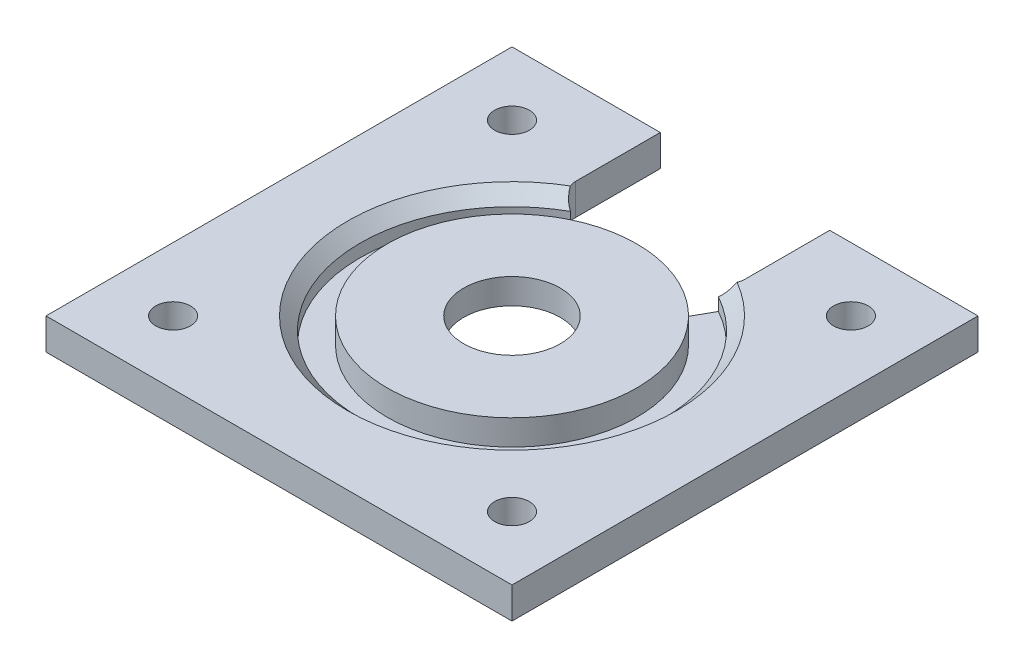
SolidWorks part; units mm, degrees
ref_plane "Front Plane" through (0, 0, 0) normal (0, 0, 1) x (1, 0, 0)
ref_plane "Top Plane" through (0, 0, 0) normal (0, 1, 0) x (1, 0, 0)
ref_plane "Right Plane" through (0, 0, 0) normal (1, 0, 0) x (0, 0, -1)
sketch "Sketch1" plane through (0, 0, 0) normal (0, 0, 1) x (1, 0, 0)
  line L0 (0, 0) -> (5.8, 0)
  line L1 (5.8, 0) -> (5.8, -0.7)
  line L2 (5.8, -0.7) -> (19.7672, -0.7)
  line L3 (19.7672, -0.7) -> (19.7672, 0)
  line L4 (19.7672, 0) -> (9.03, 0)
  line L5 (9.03, 0) -> (9.03, 3)
  line L6 (9.03, 3) -> (0, 3)
  line L7 (0, 3) -> (0, 0)
  line L8 (-5.7, -3.5493) -> (-5.7, 12.6338) construction
  line L9 (-11.4, 3) -> (-11.4, 0)
  line L10 (-20.43, 3) -> (-11.4, 3)
  line L11 (-20.43, 0) -> (-20.43, 3)
  line L12 (-31.1672, 0) -> (-20.43, 0)
  line L13 (-31.1672, -0.7) -> (-31.1672, 0)
  line L14 (-17.2, -0.7) -> (-31.1672, -0.7)
  line L15 (-17.2, 0) -> (-17.2, -0.7)
  line L16 (-11.4, 0) -> (-17.2, 0)
  dimension "D1" = 3
  dimension "D2" = 11.4
  dimension "D3" = 9.03
  dimension "D4" = 0.7
  dimension "D5" = 23
  dimension "D6" = 3
revolve "Revolve1" add sketch "Sketch1" angle 360 about L8
sketch "Sketch2" plane through (0, 0, 0) normal (0, 1, 0) x (1, 0, 0)
  line L5 (-33.2, -27.5) -> (21.8, 27.5) construction
  line L6 (-33.2, 27.5) -> (21.8, -27.5) construction
  line L7 (-33.2, 27.5) -> (21.8, 27.5)
  line L8 (-33.2, 27.5) -> (-33.2, -27.5)
  line L9 (-33.2, -27.5) -> (21.8, -27.5)
  line L10 (21.8, 27.5) -> (21.8, -27.5)
  circle A0 centre (-5.7, 0) radius 17.1
  circle A2 centre (-5.7, 0) radius 5.7 construction
  dimension "D1" = 11.4
  dimension "D2" = 55
  dimension "D3" = 55
extrude "Boss-Extrude1" add sketch "Sketch2" against normal up to surface (0.7 mm away) up to face at (-5.7, -0.7, -25.4672)
sketch "Sketch3" plane through (0, 0, 0) normal (0, 1, 0) x (1, 0, 0)
  line L5 (-33.2, -27.5) -> (21.8, -27.5)
  line L6 (-33.2, -27.5) -> (-33.2, 27.5)
  line L7 (-33.2, 27.5) -> (21.8, 27.5)
  line L8 (21.8, -27.5) -> (21.8, 27.5)
  line L9 (-33.2, -27.5) -> (21.8, 27.5) construction
  line L10 (-33.2, 27.5) -> (21.8, -27.5) construction
  circle A0 centre (-5.7, 0) radius 17.905
  circle A1 centre (-5.7, 0) radius 14.73 construction
  dimension "D1" = 3.175
  dimension "D2" = 55
extrude "Boss-Extrude2" add sketch "Sketch3" along normal up to surface (3 mm away) up to face at (-5.7, 3, -5.7)
sketch "Sketch5" plane through (0, 3, 0) normal (0, 1, 0) x (1, 0, 0)
  line L1 (-25.7, -20) -> (14.3, -20) construction
  line L2 (-25.7, -20) -> (-25.7, 20) construction
  line L3 (-25.7, 20) -> (14.3, 20) construction
  line L4 (14.3, -20) -> (14.3, 20) construction
  line L5 (-25.7, -20) -> (14.3, 20) construction
  line L6 (-25.7, 20) -> (14.3, -20) construction
  circle A0 centre (14.3, 20) radius 2.05
  circle A1 centre (-25.7, 20) radius 2.05
  circle A2 centre (-25.7, -20) radius 2.05
  circle A3 centre (14.3, -20) radius 2.05
  point P0 (-5.7, 0)
  dimension "D1" = 4.1
  dimension "D2" = 40
extrude "Cut-Extrude1" cut sketch "Sketch5" against normal blind 10
chamfer "Chamfer1" distance 1.5 angle 45 1 edges at (-5.7, 3, 17.905)
sketch "Sketch6" plane through (0, 3, 0) normal (0, 1, 0) x (1, 0, 0)
  circle A0 centre (14.3, 20) radius 4.5
  circle A1 centre (14.3, -20) radius 4.5
  circle A2 centre (-25.7, -20) radius 4.5
  circle A3 centre (-25.7, 20) radius 4.5
  point P12 (-5.7, 0)
  dimension "D2" = 9
  dimension "D1" = 4
extrude "Cut-Extrude2" [suppressed] cut sketch "Sketch6" against normal blind 1
sketch "Sketch7" plane through (0, 3, 0) normal (0, 1, 0) x (1, 0, 0)
  line L0 (-5.7, 0) -> (-5.7, 27.5) construction
  line L1 (21.8, 27.5) -> (-33.2, 27.5) construction
  line L3 (-15.7, 17.5) -> (-15.7, 27.5)
  line L4 (4.3, 17.5) -> (4.3, 27.5)
  line L5 (-15.7, 27.5) -> (4.3, 27.5)
  line L6 (2.3, 15.5) -> (-13.7, 15.5)
  arc A2 (4.3, 17.5) -> (2.3, 15.5) centre (2.3, 17.5) cw
  arc A3 (-15.7, 17.5) -> (-13.7, 15.5) centre (-13.7, 17.5) ccw
  dimension "D3" = 2
  dimension "D1" = 20
  dimension "D2" = 12
extrude "Cut-Extrude3" cut sketch "Sketch7" against normal up to surface (3.7 mm away)
sketch "Sketch8" plane through (0, 0, 0) normal (0, 1, 0) x (1, 0, 0)
  line L0 (1.4772, 12.8631) -> (3.0243, 15.6357)
  line L1 (3.0243, 15.6357) -> (-14.4243, 15.6357)
  line L2 (-14.4243, 15.6357) -> (-12.8772, 12.8631)
  arc A0 (1.4772, 12.8631) -> (-12.8772, 12.8631) centre (-5.7, 0) ccw
extrude "Cut-Extrude4" cut sketch "Sketch8" against normal up to surface (0.7 mm away)
